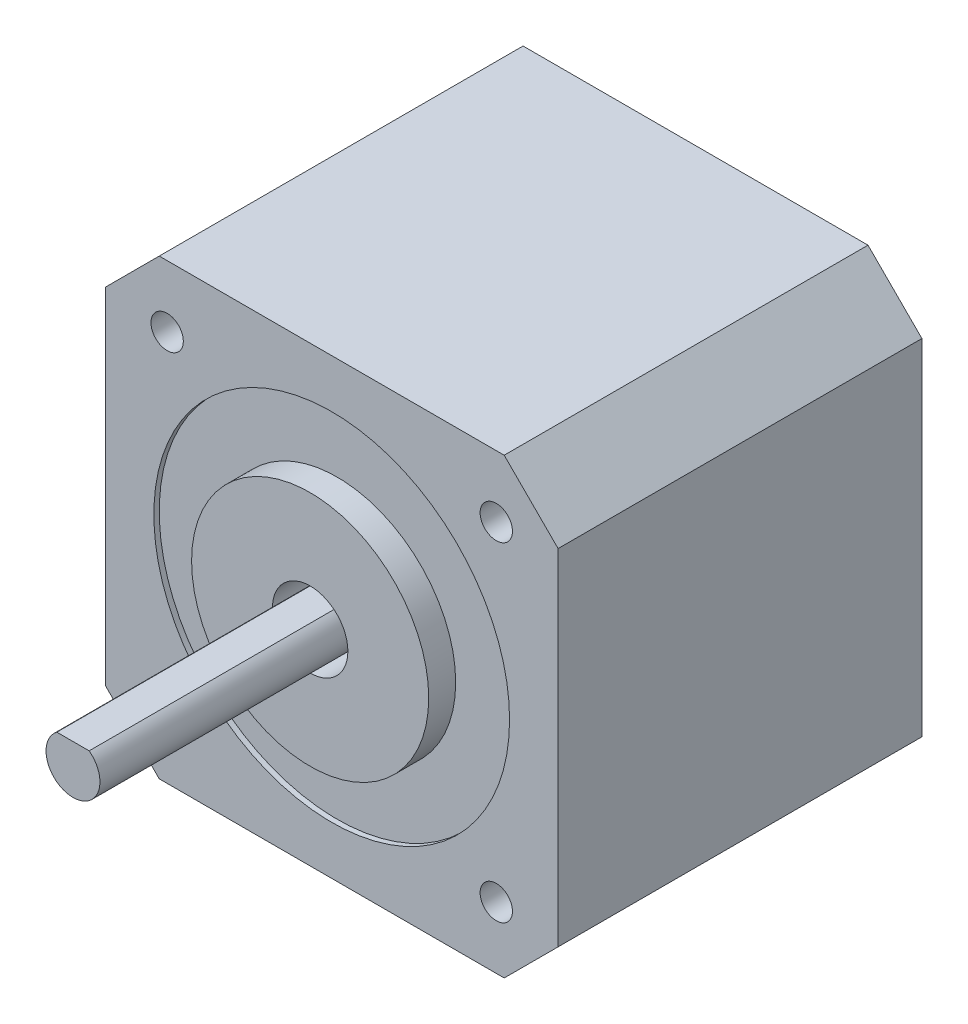
SolidWorks part; units mm, degrees
ref_plane "Front Plane" through (0, 0, 0) normal (0, 0, 1) x (1, 0, 0)
ref_plane "Top Plane" through (0, 0, 0) normal (0, 1, 0) x (1, 0, 0)
ref_plane "Right Plane" through (0, 0, 0) normal (1, 0, 0) x (0, 0, -1)
sketch "Sketch1" plane through (0, 0, 0) normal (0, 0, 1) x (1, 0, 0)
  line L0 (-34.9808, 45.6385) -> (-39.9808, 40.6385)
  line L1 (-34.9808, 45.6385) -> (-2.9808, 45.6385)
  line L2 (-39.9808, 40.6385) -> (-39.9808, 8.6385)
  line L3 (-34.9808, 3.6385) -> (-2.9808, 3.6385)
  line L4 (2.0192, 40.6385) -> (2.0192, 8.6385)
  line L5 (-2.9808, 45.6385) -> (2.0192, 40.6385)
  line L6 (2.0192, 8.6385) -> (-2.9808, 3.6385)
  line L7 (-39.9808, 8.6385) -> (-34.9808, 3.6385)
  point P0 (-39.9808, 45.6385)
  point P1 (2.0192, 3.6385)
  point P2 (-39.9808, 3.6385)
  point P3 (2.0192, 45.6385)
  dimension "D1" = 42
  dimension "D2" = 42
extrude "Boss-Extrude1" add sketch "Sketch1" along normal blind 33.75
sketch "Sketch2" plane through (0, 0, 33.75) normal (0, 0, 1) x (1, 0, 0)
  line L0 (-39.9808, 40.6385) -> (-39.9808, 8.6385) construction
  line L1 (-2.9808, 45.6385) -> (-34.9808, 45.6385) construction
  circle A0 centre (-18.9808, 24.6385) radius 16.5
  dimension "D1" = 33
  dimension "D2" = 21
  dimension "D3" = 21
extrude "Cut-Extrude1" cut sketch "Sketch2" against normal blind 0.5 contours A0
sketch "Sketch3" plane through (0, 0, 33.25) normal (0, 0, 1) x (1, 0, 0)
  circle A0 centre (-18.9808, 24.6385) radius 11
  dimension "D1" = 22
extrude "Boss-Extrude2" add sketch "Sketch3" along normal blind 2.5
sketch "Sketch4" plane through (0, 0, 35.75) normal (0, 0, 1) x (1, 0, 0)
  circle A0 centre (-18.9808, 24.6385) radius 3.5
  dimension "D1" = 7
extrude "Cut-Extrude2" cut sketch "Sketch4" against normal blind 5
sketch "Sketch5" plane through (0, 0, 30.75) normal (0, 0, 1) x (1, 0, 0)
  line L0 (-20.4808, 26.6385) -> (-17.4808, 26.6385)
  arc A0 (-20.4808, 26.6385) -> (-17.4808, 26.6385) centre (-18.9808, 24.6385) ccw
  dimension "D1" = 5
  dimension "D2" = 3
extrude "Boss-Extrude3" add sketch "Sketch5" along normal blind 27
sketch "Sketch6" plane through (0, 0, 33.75) normal (0, 0, 1) x (1, 0, 0)
  line L1 (-34.2473, 39.9049) -> (-3.7144, 39.9049) construction
  line L2 (-34.2473, 39.9049) -> (-34.2473, 9.3721) construction
  line L3 (-34.2473, 9.3721) -> (-3.7144, 9.3721) construction
  line L4 (-3.7144, 39.9049) -> (-3.7144, 9.3721) construction
  circle A0 centre (-18.9808, 24.6385) radius 21.59 construction
  circle A1 centre (-34.2473, 39.9049) radius 1.5
  circle A2 centre (-3.7144, 39.9049) radius 1.5
  circle A3 centre (-3.7144, 9.3721) radius 1.5
  circle A4 centre (-34.2473, 9.3721) radius 1.5
  dimension "D1" = 43.18
  dimension "D2" = 3
  dimension "D3" = 3
  dimension "D4" = 3
  dimension "D5" = 3
extrude "Cut-Extrude3" cut sketch "Sketch6" against normal blind 5 contours A4 | A3 | A1 | A2
ref_plane "Plane1" through (0, 0, 16.875) normal (0, 0, -1) x (-1, 0, 0)
mirror "Mirror1" about plane through (0, 0, 16.875) normal (0, 0, -1) of "Cut-Extrude3"
